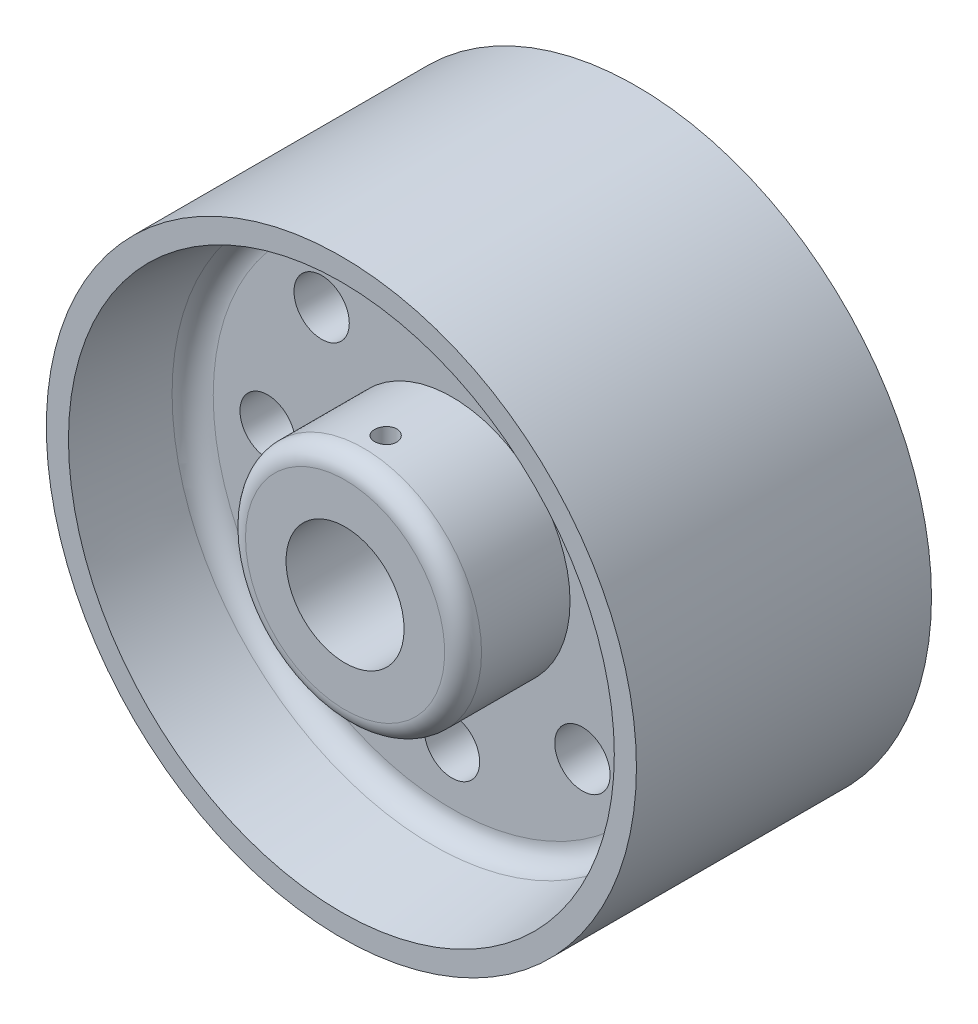
SolidWorks part; units mm, degrees
ref_plane "Front Plane" through (0, 0, 0) normal (0, 0, 1) x (1, 0, 0)
ref_plane "Top Plane" through (0, 0, 0) normal (0, 1, 0) x (1, 0, 0)
ref_plane "Right Plane" through (0, 0, 0) normal (1, 0, 0) x (0, 0, -1)
other "Configuration Table"
sketch "Sketch1" plane through (0, 0, 0) normal (1, 0, 0) x (0, 0, -1)
  line L0 (-30, 0) -> (10, 0) construction
  line L1 (0, 8) -> (0, 40)
  line L2 (0, 40) -> (-20, 40)
  line L3 (-20, 40) -> (-20, 37)
  line L4 (-20, 37) -> (-5, 35)
  line L5 (-5, 35) -> (-5, 16)
  line L6 (-5, 16) -> (-19.5, 16)
  line L7 (-19.5, 16) -> (-19.5, 8)
  line L8 (-19.5, 8) -> (0, 8)
  dimension "D1" = 16
  dimension "D2" = 32
  dimension "D3" = 80
  dimension "D4" = 3
  dimension "D5" = 5
  dimension "D6" = 5
  dimension "D7" = 20
  dimension "D8" = 19.5
revolve "Revolve1" add sketch "Sketch1" angle 360 about L0
sketch "Sketch2" plane through (0, 0, 5) normal (0, 0, 1) x (1, 0, 0)
  circle A0 centre (0, 25) radius 3.75
  circle A1 centre (17.6777, 17.6777) radius 3.75
  circle A2 centre (25, 0) radius 3.75
  circle A3 centre (17.6777, -17.6777) radius 3.75
  circle A4 centre (0, -25) radius 3.75
  circle A5 centre (-17.6777, -17.6777) radius 3.75
  circle A6 centre (-25, 0) radius 3.75
  circle A7 centre (-17.6777, 17.6777) radius 3.75
  dimension "D1" = 25
  dimension "D2" = 7.5
extrude "Cut-Extrude1" cut sketch "Sketch2" against normal through all
sketch "Sketch3" plane through (0, 0, 0) normal (0, 1, 0) x (1, 0, 0)
  line L1 (-40, -20) -> (40, -20) construction
  circle A0 centre (0, -14) radius 1.5
  dimension "D1" = 3
  dimension "D2" = 6
extrude "Cut-Extrude2" cut sketch "Sketch3" along normal up to next
fillet "Fillet1" radius 3 1 edges at (35, 0, 5)
fillet "Fillet3" radius 2.5 1 edges at (16, 0, 19.5)
mirror "Mirror1" about plane through (0, 0, 0) normal (0, 0, 1) of "Fillet3", "Fillet1", "Cut-Extrude2", "Cut-Extrude1", "Revolve1"
